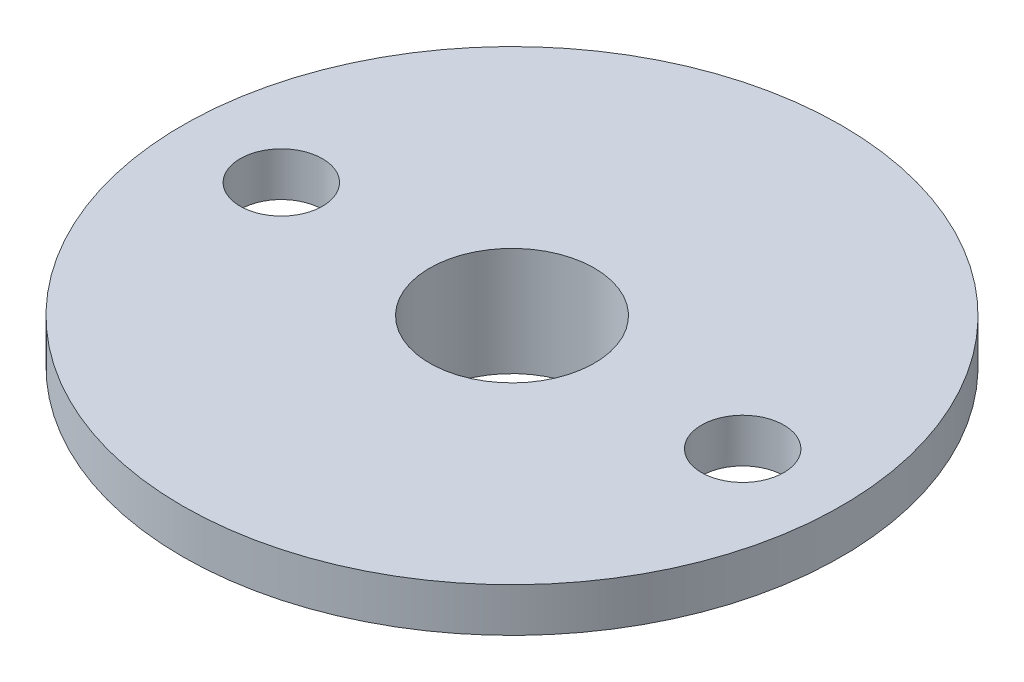
SolidWorks part; units mm, degrees
material "1060 Alloy"
ref_plane "Front Plane" through (0, 0, 0) normal (0, 0, 1) x (1, 0, 0)
ref_plane "Top Plane" through (0, 0, 0) normal (0, 1, 0) x (1, 0, 0)
ref_plane "Right Plane" through (0, 0, 0) normal (1, 0, 0) x (0, 0, -1)
sketch "Sketch1" plane through (0, 0, 0) normal (0, 0, 1) x (1, 0, 0)
  line L0 (0, 0) -> (0, 50000) construction
  line L3 (12, 0) -> (12, -1.6)
  line L4 (12, -1.6) -> (5, -1.6)
  line L5 (5, -1.6) -> (5, -3.95)
  line L6 (5, -3.95) -> (3, -3.95)
  line L8 (3, 0) -> (12, 0)
  line L9 (8.4, -1.6) -> (8.4, 0) construction
  line L10 (14.3, 0) -> (-14.3, 0) construction
  line L11 (3, -3.95) -> (3, 0)
  dimension "D1" = 24
  dimension "D2" = 10
  dimension "D3" = 1.6
  dimension "D4" = 8.4
  dimension "D5" = 2.35
  dimension "D6" = 3
revolve "Revolve1" add sketch "Sketch1" angle 360 about L0
sketch "Sketch2" plane through (0, 0, 0) normal (0, 1, 0) x (1, 0, 0)
  line L0 (0, 12) -> (0, -12) construction
  line L1 (0, -55) -> (0, 55) construction
  circle A0 centre (8.4, 0) radius 1.5
  circle A1 centre (0, 0) radius 12 construction
  circle A2 centre (-8.4, 0) radius 1.5
  dimension "D1" = 3
extrude "Cut-Extrude1" cut sketch "Sketch2" against normal through all
